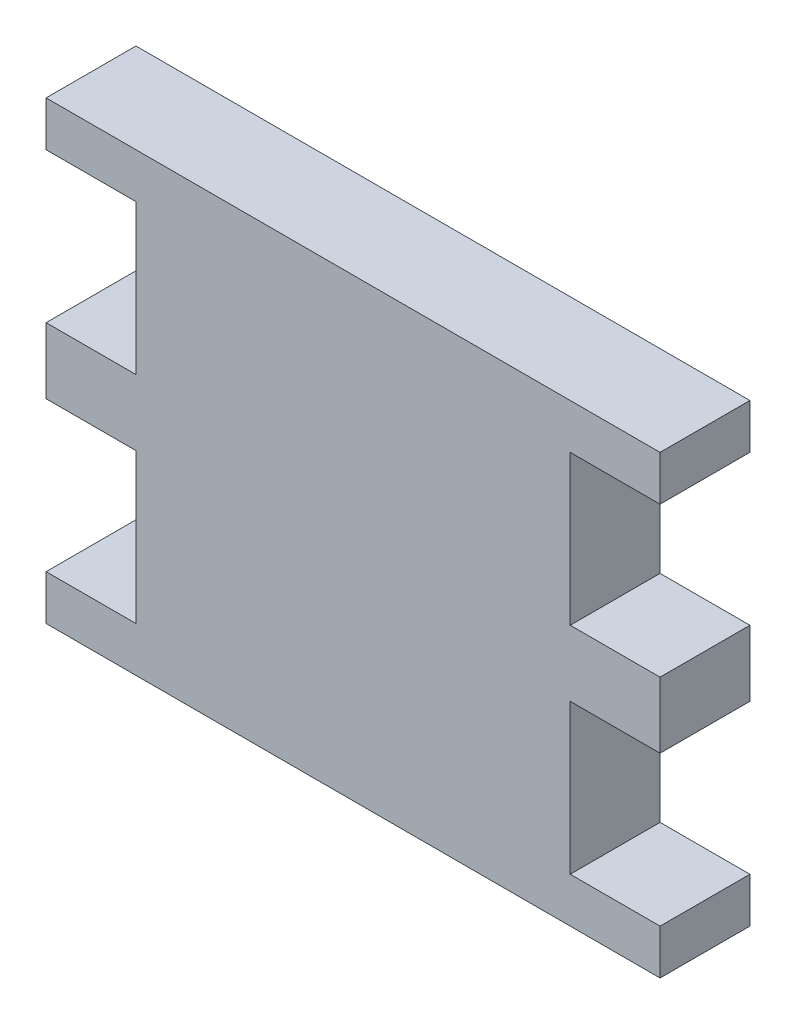
SolidWorks part; units mm, degrees
ref_plane "Plan de face" through (0, 0, 0) normal (0, 0, 1) x (1, 0, 0)
ref_plane "Plan de dessus" through (0, 0, 0) normal (0, 1, 0) x (1, 0, 0)
ref_plane "Plan de droite" through (0, 0, 0) normal (1, 0, 0) x (0, 0, -1)
sketch "Esquisse1" plane through (0, 0, 0) normal (0, 0, 1) x (1, 0, 0)
  line L0 (-20.5, 14.5114) -> (20.5, 14.5114)
  line L1 (-20.5, 14.5114) -> (-20.5, 11.5114)
  line L2 (-20.5, -15.8886) -> (20.5, -15.8886)
  line L3 (-20.5, 1.5114) -> (-20.5, -2.8886)
  line L4 (-20.5, 11.5114) -> (-14.5, 11.5114)
  line L5 (-14.5, 11.5114) -> (-14.5, 1.5114)
  line L6 (-14.5, 1.5114) -> (-20.5, 1.5114)
  line L7 (-20.5, -2.8886) -> (-14.5, -2.8886)
  line L8 (-14.5, -2.8886) -> (-14.5, -12.8886)
  line L9 (-14.5, -12.8886) -> (-20.5, -12.8886)
  line L10 (-20.5, -12.8886) -> (-20.5, -15.8886)
  line L11 (0, 26.0896) -> (0, -25.0308) construction
  line L12 (20.5, -12.8886) -> (20.5, -15.8886)
  line L13 (14.5, -12.8886) -> (20.5, -12.8886)
  line L14 (14.5, -2.8886) -> (14.5, -12.8886)
  line L15 (20.5, -2.8886) -> (14.5, -2.8886)
  line L16 (14.5, 1.5114) -> (20.5, 1.5114)
  line L17 (20.5, 1.5114) -> (20.5, -2.8886)
  line L18 (20.5, 14.5114) -> (20.5, 11.5114)
  line L19 (14.5, 11.5114) -> (14.5, 1.5114)
  line L20 (20.5, 11.5114) -> (14.5, 11.5114)
  point P2 (0, 14.5114)
  point P25 (0, -15.8886)
  dimension "D1" = 30.4
  dimension "D2" = 3
  dimension "D3" = 3
  dimension "D4" = 6
  dimension "D5" = 10
  dimension "D6" = 10
  dimension "D7" = 6
  dimension "D8" = 41
  dimension "D9" = 20.5
  dimension "D10" = 6
extrude "Boss.-Extru.1" add sketch "Esquisse1" along normal blind 6
